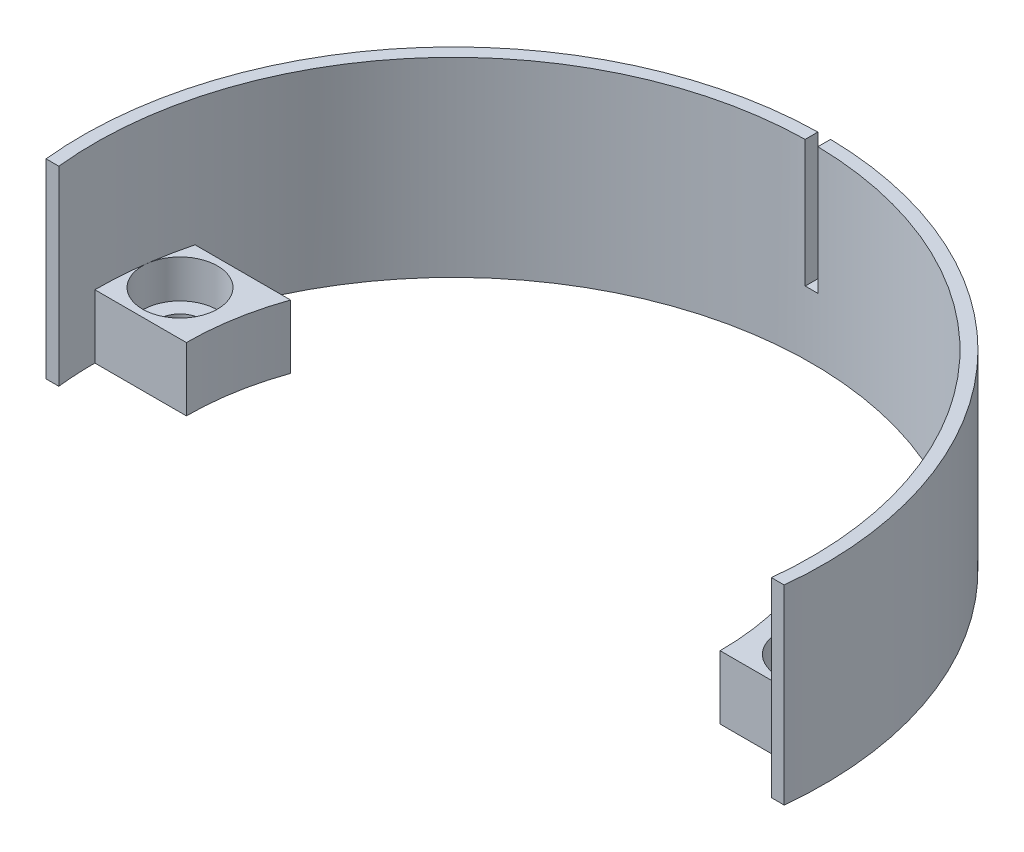
SolidWorks part; units mm, degrees
material "PLA"
ref_plane "Alzado" through (0, 0, 0) normal (0, 0, 1) x (1, 0, 0)
ref_plane "Planta" through (0, 0, 0) normal (0, 1, 0) x (1, 0, 0)
ref_plane "Vista lateral" through (0, 0, 0) normal (1, 0, 0) x (0, 0, -1)
sketch "Croquis1" plane through (0, 0, 0) normal (0, 1, 0) x (1, 0, 0)
  line L0 (-29.0455, -3) -> (-28.04, -3)
  line L1 (28.04, -3) -> (29.0455, -3)
  line L2 (-28.2, 0) -> (-21, 0)
  line L3 (-27.3174, 7) -> (-19.799, 7)
  line L4 (21, 0) -> (28.2, 0)
  line L5 (19.799, 7) -> (27.3174, 7)
  arc A0 (29.0455, -3) -> (-29.0455, -3) centre (0, 0) ccw
  arc A1 (28.04, -3) -> (28.2, 0) centre (0, 0) ccw
  arc A2 (-19.799, 7) -> (-21, 0) centre (0, 0) ccw
  arc A3 (21, 0) -> (19.799, 7) centre (0, 0) ccw
  circle A4 centre (-25, 3.5) radius 1.7
  circle A5 centre (25, 3.5) radius 1.7
  arc A6 (-28.2, 0) -> (-28.04, -3) centre (0, 0) ccw
  arc A7 (27.3174, 7) -> (-27.3174, 7) centre (0, 0) ccw
  dimension "D1" = 58.4
  dimension "D2" = 56.4
  dimension "D4" = 21
  dimension "D9" = 3.4
  dimension "D3" = 3
  dimension "D5" = 7
  dimension "D6" = 3.5
  dimension "D7" = 25
  dimension "D8" = 25
extrude "Saliente-Extruir1" add sketch "Croquis1" along normal blind 5
sketch "Croquis2" plane through (0, 5, 0) normal (0, 1, 0) x (1, 0, 0)
  line L0 (28.04, -3) -> (29.0455, -3) construction
  line L1 (-29.0455, -3) -> (-28.04, -3) construction
  line L2 (28.04, -3) -> (29.0455, -3)
  line L3 (-29.0455, -3) -> (-28.04, -3)
  line L4 (-0.5, 29.1957) -> (-0.5, 28.1956)
  line L5 (0.5, 29.1957) -> (0.5, 28.1956)
  arc A0 (29.0455, -3) -> (-29.0455, -3) centre (0, 0) ccw construction
  arc A1 (29.0455, -3) -> (0.5, 29.1957) centre (0, 0) ccw
  arc A2 (-28.04, -3) -> (-0.5, 28.1956) centre (0, 0) cw
  arc A3 (0.5, 28.1956) -> (28.04, -3) centre (0, 0) cw
  arc A4 (-0.5, 29.1957) -> (-29.0455, -3) centre (0, 0) ccw
  dimension "D1" = 1
  dimension "D2" = 0.5
extrude "Saliente-Extruir2" add sketch "Croquis2" along normal blind 10
sketch "Croquis3" plane through (0, 5, 0) normal (0, 1, 0) x (1, 0, 0)
  circle A0 centre (-25, 3.5) radius 2.95
  circle A1 centre (25, 3.5) radius 2.95
  dimension "D1" = 5.9
extrude "Cortar-Extruir1" cut sketch "Croquis3" against normal blind 3
